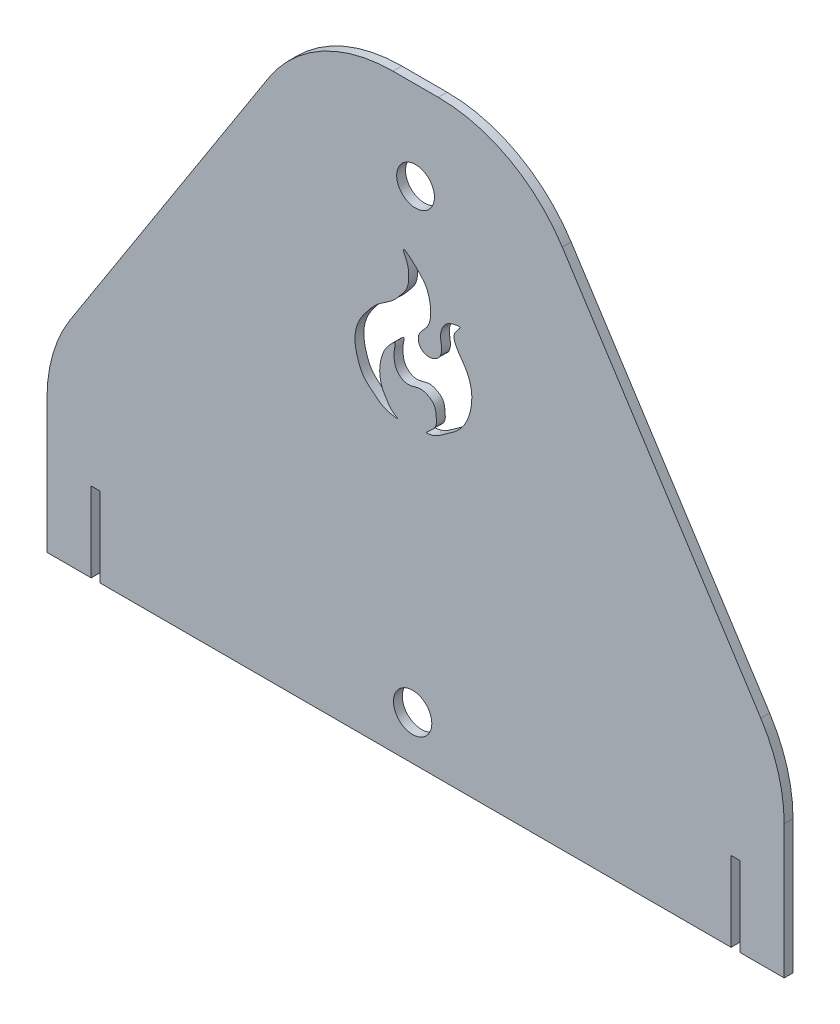
SolidWorks part; units mm, degrees
ref_plane "Alzado" through (0, 0, 0) normal (0, 0, 1) x (1, 0, 0)
ref_plane "Planta" through (0, 0, 0) normal (0, 1, 0) x (1, 0, 0)
ref_plane "Vista lateral" through (0, 0, 0) normal (1, 0, 0) x (0, 0, -1)
sketch "Croquis1" plane through (0, 0, 0) normal (0, 0, 1) x (1, 0, 0)
  line L0 (-125, -40) -> (-35, 100)
  line L1 (-125, 100) -> (125, 100)
  line L2 (-125, 100) -> (-125, -100)
  line L3 (-125, -100) -> (125, -100)
  line L4 (125, 100) -> (125, -100)
  line L5 (-125, 100) -> (125, -100) construction
  line L6 (-125, -100) -> (125, 100) construction
  line L7 (35, 100) -> (125, -40)
  circle A0 centre (0, 70) radius 6.4
  point P0 (0, 0)
  dimension "D7" = 12.8
  dimension "D1" = 200
  dimension "D2" = 250
  dimension "D3" = 60
  dimension "D4" = 90
  dimension "D5" = 60
  dimension "D6" = 90
  dimension "D8" = 35
  dimension "D9" = 30
extrude "Saliente-Extruir1" add sketch "Croquis1" along normal blind 3 contours L7 L1 L0 L2 L3 L4
fillet "Redondeo1" radius 50 4 edges at (-125, -40, 1.5) (125, -40, 1.5) (35, 100, 1.5) (-35, 100, 1.5)
sketch "Croquis3" plane through (0, 0, 3) normal (0, 0, 1) x (1, 0, 0)
  line L0 (-125, -100) -> (125, -100) construction
  line L1 (-110, -100) -> (-107, -100)
  line L2 (-110, -100) -> (-110, -73)
  line L3 (-110, -73) -> (-107, -73)
  line L4 (-107, -100) -> (-107, -73)
  line L5 (-125, -54.6851) -> (-125, -100) construction
  line L6 (125, -54.6851) -> (125, -100) construction
  line L7 (110, -100) -> (107, -100)
  line L8 (110, -100) -> (110, -73)
  line L9 (110, -73) -> (107, -73)
  line L10 (107, -100) -> (107, -73)
  dimension "D1" = 27
  dimension "D2" = 3
  dimension "D3" = 15
  dimension "D4" = 27
  dimension "D5" = 3
  dimension "D6" = 15
extrude "Cortar-Extruir2" cut sketch "Croquis3" against normal through all
sketch "Croquis4" plane through (0, 0, 3) normal (0, 0, 1) x (1, 0, 0)
  spline S0 degree 3 poles (-2.5615, 46.0235) (-5.7847, 51.728) (2.3965, 44.6255) (4.4998, 40.9346) (5.5159, 35.09) (4.2991, 30.411) (1.4455, 28.2991) (0.6457, 25.5574) (1.5655, 23.2149) (3.7588, 21.9908) (6.2964, 22.2985) (8.8018, 24.1343) (8.9028, 27.5361) (8.1243, 30.8219) (9.5457, 34.4085) (11.8692, 35.7996) (15.9553, 36.6231) (13.6697, 34.3507) (12.6564, 32.4524) (14.0512, 28.8368) (17.0836, 25.4045) (19.2949, 19.8982) (18.9977, 13.8219) (17.0495, 8.3673) (13.4298, 4.3985) (9.5045, 2.095) (7.1397, -0.0207) (2.0164, -1.0922) (7.3067, 2.1087) (7.0084, 5.538) (6.7957, 8.9513) (4.2538, 10.798) (1.5473, 11.6842) (-0.7, 10.7532) (-2.7292, 10.5037) (-4.4955, 10.9188) (-5.9783, 12.1507) (-7.0191, 13.8412) (-7.1575, 15.169) (-7.3548, 16.4626) (-7.3293, 18.2642) (-6.447, 21.6013) (-10.0617, 17.8134) (-11.1924, 15.3992) (-12.1709, 11.732) (-12.2211, 8.3269) (-11.4717, 5.0312) (-9.5834, 2.2707) (-8.5244, 0.1995) (-4.8543, -1.7006) (-10.8968, -0.6372) (-13.5548, 1.678) (-17.9995, 5.0786) (-19.8431, 10.0023) (-21.0144, 15.325) (-19.5571, 21.0626) (-16.139, 25.5373) (-12.5493, 29.6769) (-8.0168, 31.959) (-5.105, 35.472) (-2.4654, 38.6612) (-2.2236, 42.7832) (-2.5615, 46.0235) (-5.7847, 51.728) (2.3965, 44.6255) knots -0.040077 -0.024587 -0.011114 0 0.031004 0.060687 0.089933 0.112423 0.130059 0.140778 0.153022 0.164926 0.175677 0.190181 0.207268 0.22252 0.241754 0.257857 0.269984 0.279657 0.290002 0.304323 0.331994 0.360844 0.390196 0.421995 0.445705 0.470225 0.487265 0.500608 0.520143 0.535921 0.554344 0.567339 0.580571 0.595399 0.602338 0.611213 0.621781 0.630602 0.640133 0.642296 0.65223 0.659039 0.669932 0.686357 0.698409 0.710639 0.725152 0.735995 0.747276 0.754938 0.766749 0.785853 0.807016 0.824714 0.844774 0.868058 0.88884 0.908343 0.929635 0.944914 0.959923 0.975413 0.988886 1 1.031004 1.060687 1.089933 only from (-4.1273, 49.0959) to (-4.1273, 49.0959)
extrude "Cortar-Extruir3" cut sketch "Croquis4" along direction (0, 0, 1) on the side against the normal through all
sketch "Croquis5" plane through (0, 0, 3) normal (0, 0, 1) x (1, 0, 0)
  line L0 (-107, -100) -> (107, -100) construction
  line L1 (-125, -54.6851) -> (-125, -100) construction
  circle A0 centre (-1, -85) radius 6.5
  dimension "D1" = 13
  dimension "D2" = 15
  dimension "D3" = 124
extrude "Cortar-Extruir4" cut sketch "Croquis5" against normal through all
